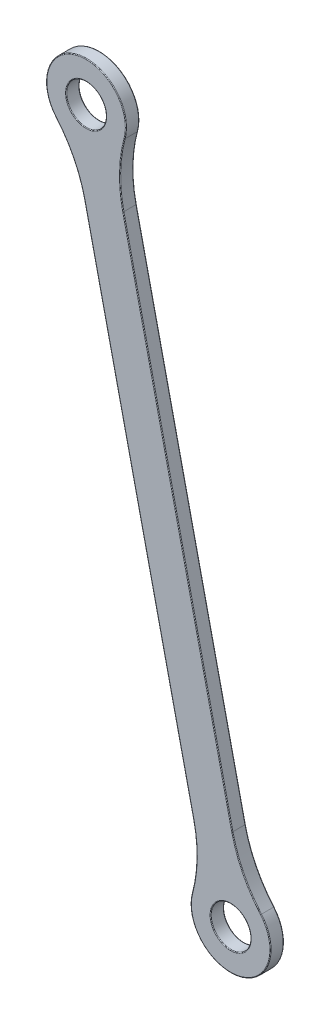
SolidWorks part; units mm, degrees
ref_plane "Płaszczyzna przednia" through (0, 0, 0) normal (0, 0, 1) x (1, 0, 0)
ref_plane "Płaszczyzna górna" through (0, 0, 0) normal (0, 1, 0) x (1, 0, 0)
ref_plane "Płaszczyzna prawa" through (0, 0, 0) normal (1, 0, 0) x (0, 0, -1)
sketch "Szkic1" plane through (0, 0, 0) normal (0, 0, 1) x (1, 0, 0)
  line L0 (14.5, 81.5) -> (-18.1175, 225.861) construction
  line L1 (14.5, 81.5) -> (-18.1175, 225.861) construction
sketch "Szkic2" plane through (0, 0, 0) normal (0, 0, 1) x (1, 0, 0)
  line L0 (14.5, 81.5) -> (-18.1175, 225.861) construction
  line L1 (14.5, 81.5) -> (-18.1175, 225.861) construction
  line L2 (10.1106, 80.5083) -> (-22.5069, 224.8692)
  line L3 (18.8894, 82.4917) -> (-13.7282, 226.8527)
  circle A0 centre (-18.1175, 225.861) radius 9 construction
  circle A1 centre (14.5, 81.5) radius 9 construction
  arc A2 (10.1106, 80.5083) -> (18.8894, 82.4917) centre (14.5, 81.5) ccw
  arc A3 (-13.7282, 226.8527) -> (-22.5069, 224.8692) centre (-18.1175, 225.861) ccw
  arc A4 (-13.7282, 226.8527) -> (-22.5069, 224.8692) centre (-18.1175, 225.861) cw
  arc A5 (18.8894, 82.4917) -> (10.1106, 80.5083) centre (14.5, 81.5) ccw
  arc A6 (-12.0104, 219.2502) -> (-20.7891, 217.2667) centre (-18.1175, 225.861) ccw
  arc A7 (17.1716, 90.0943) -> (8.3929, 88.1108) centre (14.5, 81.5) cw
  point P7 (-1.8088, 153.6805)
  point P26 (0, 0)
  dimension "D1" = 18
  dimension "D2" = 18
  dimension "D3" = 9
extrude "Dodanie-wyciągnięcie1" add sketch "Szkic2" against normal blind 3 contours A5 L3 A4 L2 | A7 L3 A2 L2 | L3 A6 L2 A3
fillet "Zaokrąglenie1" radius 30 1 edges at (-20.7891, 217.2667, -1.5)
fillet "Zaokrąglenie2" radius 30 1 edges at (-12.0104, 219.2502, -1.5)
fillet "Zaokrąglenie3" radius 30 1 edges at (8.3929, 88.1108, -1.5)
fillet "Zaokrąglenie4" radius 30 1 edges at (17.1716, 90.0943, -1.5)
fillet "Zaokrąglenie5" radius 0.15 20 edges at (19, 81.5, 0) (-13.6175, 225.861, 0) (6.834, 91.0255, 0) (-6.1981, 152.6887, 0) (-20.9435, 213.9649, 0) (-20.101, 234.6397, 0) (-10.4515, 216.3355, 0) (2.5806, 154.6722, 0) (17.326, 93.3961, 0) (16.4835, 72.7213, 0) (19, 81.5, -3) (-13.6175, 225.861, -3) (-10.4515, 216.3355, -3) (-20.101, 234.6397, -3) (-20.9435, 213.9649, -3) (-6.1981, 152.6887, -3) (6.834, 91.0255, -3) (16.4835, 72.7213, -3) (17.326, 93.3961, -3) (2.5806, 154.6722, -3)
